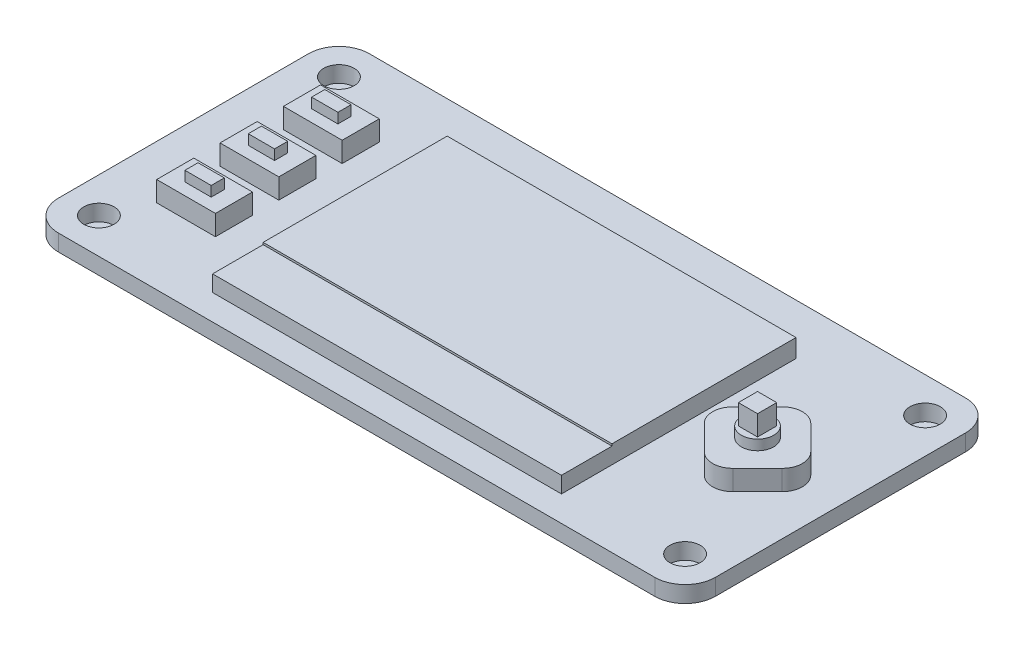
SolidWorks part; units mm, degrees
ref_plane "前视基准面" through (0, 0, 0) normal (0, 0, 1) x (1, 0, 0)
ref_plane "上视基准面" through (0, 0, 0) normal (0, 1, 0) x (1, 0, 0)
ref_plane "右视基准面" through (0, 0, 0) normal (1, 0, 0) x (0, 0, -1)
sketch "草图1" plane through (0, 0, 0) normal (0, 1, 0) x (1, 0, 0)
  line L1 (-29.5, 15.375) -> (29.5, 15.375)
  line L2 (-32.5, 12.375) -> (-32.5, -12.375)
  line L3 (-29.5, -15.375) -> (29.5, -15.375)
  line L4 (32.5, 12.375) -> (32.5, -12.375)
  line L5 (-32.5, 15.375) -> (32.5, -15.375) construction
  line L6 (-32.5, -15.375) -> (32.5, 15.375) construction
  arc A0 (-32.5, -12.375) -> (-29.5, -15.375) centre (-29.5, -12.375) ccw
  arc A1 (29.5, -15.375) -> (32.5, -12.375) centre (29.5, -12.375) ccw
  arc A2 (29.5, 15.375) -> (32.5, 12.375) centre (29.5, 12.375) cw
  arc A3 (-29.5, 15.375) -> (-32.5, 12.375) centre (-29.5, 12.375) ccw
  point P0 (0, 0)
  dimension "D3" = 3
  dimension "D1" = 30.75
  dimension "D2" = 65
extrude "凸台-拉伸1" add sketch "草图1" along normal blind 1.63
sketch "草图2" plane through (0, 1.63, 0) normal (0, 1, 0) x (1, 0, 0)
  line L0 (29.5, 15.375) -> (-29.5, 15.375) construction
  line L2 (-32.5, 12.375) -> (-32.5, -12.375) construction
  line L3 (-29.5, -15.375) -> (29.5, -15.375) construction
  line L4 (32.5, -12.375) -> (32.5, 12.375) construction
  circle A0 centre (-29, 11.875) radius 1.5
  circle A1 centre (-29, -11.875) radius 1.5
  circle A2 centre (29, -11.875) radius 1.5
  circle A3 centre (29, 11.875) radius 1.5
  dimension "D1" = 3
  dimension "D2" = 3.5
  dimension "D3" = 3.5
  dimension "D4" = 3.5
  dimension "D5" = 3.5
extrude "切除-拉伸1" cut sketch "草图2" against normal blind 1.6
sketch "草图3" plane through (0, 1.63, 0) normal (0, 1, 0) x (1, 0, 0)
  line L0 (-29.5, -15.375) -> (29.5, -15.375) construction
  line L1 (-16.78, 10.365) -> (17.74, 10.365)
  line L2 (-16.78, 10.365) -> (-16.78, -12.845)
  line L3 (-16.78, -12.845) -> (17.74, -12.845)
  line L4 (17.74, 10.365) -> (17.74, -12.845)
  line L7 (32.5, -12.375) -> (32.5, 12.375) construction
  dimension "D1" = 23.21
  dimension "D2" = 34.52
  dimension "D3" = 2.53
  dimension "D4" = 14.76
sketch "草图4" plane through (0, 1.63, 0) normal (0, 1, 0) x (1, 0, 0)
  line L0 (-29.5, -15.375) -> (29.5, -15.375) construction
  line L1 (-27.23, 8.285) -> (-21.42, 8.285)
  line L2 (-27.23, 8.285) -> (-27.23, 4.615)
  line L3 (-27.23, 4.615) -> (-21.42, 4.615)
  line L4 (-21.42, 8.285) -> (-21.42, 4.615)
  line L5 (-27.23, 2.015) -> (-21.42, 2.015)
  line L6 (-27.23, 2.015) -> (-27.23, -1.655)
  line L7 (-27.23, -1.655) -> (-21.42, -1.655)
  line L8 (-21.42, 2.015) -> (-21.42, -1.655)
  line L9 (-27.23, -4.255) -> (-21.42, -4.255)
  line L10 (-27.23, -4.255) -> (-27.23, -7.925)
  line L11 (-27.23, -7.925) -> (-21.42, -7.925)
  line L12 (-21.42, -4.255) -> (-21.42, -7.925)
  line L13 (-32.5, 12.375) -> (-32.5, -12.375) construction
  dimension "D1" = 5.81
  dimension "D2" = 3.67
  dimension "D3" = 2.6
  dimension "D4" = 2.6
  dimension "D5" = 7.45
  dimension "D6" = 5.27
sketch "草图5" plane through (0, 1.63, 0) normal (0, 1, 0) x (1, 0, 0)
  line L0 (26.0247, 3.5383) -> (28.4642, 1.0987)
  line L1 (23.1963, 3.5383) -> (20.7567, 1.0987)
  line L2 (28.4642, -1.7297) -> (26.0247, -4.1692)
  line L3 (20.7567, -1.7297) -> (23.1963, -4.1692)
  line L4 (32.5, -12.375) -> (32.5, 12.375) construction
  line L5 (-29.5, -15.375) -> (29.5, -15.375) construction
  arc A0 (26.0247, -4.1692) -> (23.1963, -4.1692) centre (24.6105, -2.755) cw
  arc A1 (20.7567, 1.0987) -> (20.7567, -1.7297) centre (22.171, -0.3155) ccw
  arc A2 (23.1963, 3.5383) -> (26.0247, 3.5383) centre (24.6105, 2.124) cw
  arc A3 (28.4642, 1.0987) -> (28.4642, -1.7297) centre (27.05, -0.3155) cw
  point P8 (19.3425, -0.3155)
  point P11 (24.6105, 4.9525)
  point P14 (29.8784, -0.3155)
  point P15 (29.05, -0.3155)
  point P18 (24.6105, -4.755)
  dimension "D3" = 2
  dimension "D1" = 7.45
  dimension "D2" = 7.45
  dimension "D4" = 3.45
  dimension "D5" = 10.62
extrude "凸台-拉伸2" add sketch "草图3" along normal blind 1.8
extrude "凸台-拉伸3" add sketch "草图5" along normal blind 2
extrude "凸台-拉伸4" add sketch "草图4" along normal blind 2
sketch "草图7" plane through (0, 3.63, 0) normal (0, 1, 0) x (1, 0, 0)
  line L0 (-21.42, 8.285) -> (-27.23, 8.285) construction
  line L1 (-25.625, 7.1) -> (-23.025, 7.1)
  line L2 (-25.625, 7.1) -> (-25.625, 5.8)
  line L3 (-25.625, 5.8) -> (-23.025, 5.8)
  line L4 (-23.025, 7.1) -> (-23.025, 5.8)
  line L5 (-25.625, 7.1) -> (-23.025, 5.8) construction
  line L6 (-25.625, 5.8) -> (-23.025, 7.1) construction
  line L7 (-25.625, 0.83) -> (-23.025, 0.83)
  line L8 (-25.625, 0.83) -> (-25.625, -0.47)
  line L9 (-25.625, -0.47) -> (-23.025, -0.47)
  line L10 (-23.025, 0.83) -> (-23.025, -0.47)
  line L11 (-25.625, 0.83) -> (-23.025, -0.47) construction
  line L12 (-25.625, -0.47) -> (-23.025, 0.83) construction
  line L13 (-25.625, -5.44) -> (-23.025, -5.44)
  line L14 (-25.625, -5.44) -> (-25.625, -6.74)
  line L15 (-25.625, -6.74) -> (-23.025, -6.74)
  line L16 (-23.025, -5.44) -> (-23.025, -6.74)
  line L17 (-25.625, -5.44) -> (-23.025, -6.74) construction
  line L18 (-25.625, -6.74) -> (-23.025, -5.44) construction
  line L19 (-27.23, -4.255) -> (-27.23, -7.925) construction
  line L20 (-27.23, 2.015) -> (-27.23, -1.655) construction
  line L21 (-27.23, 8.285) -> (-27.23, 4.615) construction
  point P0 (-24.325, 6.45)
  point P5 (-24.325, 0.18)
  point P10 (-24.325, -6.09)
  point P18 (-24.325, 8.285)
  point P22 (-27.23, -6.09)
  point P26 (-27.23, 0.18)
  point P30 (-27.23, 6.45)
  dimension "D1" = 2.6
  dimension "D2" = 1.3
extrude "凸台-拉伸5" add sketch "草图7" along normal blind 1
sketch "草图8" plane through (0, 0, 0) normal (0, -1, 0) x (1, 0, 0)
  line L0 (29.5, -15.375) -> (-29.5, -15.375) construction
  line L1 (-25.7, -8.735) -> (25.3, -8.735)
  line L2 (-25.7, -8.735) -> (-25.7, -13.735)
  line L3 (-25.7, -13.735) -> (25.3, -13.735)
  line L4 (25.3, -8.735) -> (25.3, -13.735)
  line L5 (32.5, 12.375) -> (32.5, -12.375) construction
  dimension "D1" = 5
  dimension "D2" = 51
  dimension "D3" = 1.64
  dimension "D4" = 7.2
extrude "凸台-拉伸6" add sketch "草图8" along normal blind 3.68
sketch "草图9" plane through (0, 3.63, 0) normal (0, 1, 0) x (1, 0, 0)
  line L1 (23.6605, 0.6345) -> (25.5605, 0.6345)
  line L2 (23.6605, 0.6345) -> (23.6605, -1.2655)
  line L3 (23.6605, -1.2655) -> (25.5605, -1.2655)
  line L4 (25.5605, 0.6345) -> (25.5605, -1.2655)
  line L5 (23.6605, 0.6345) -> (25.5605, -1.2655) construction
  line L6 (23.6605, -1.2655) -> (25.5605, 0.6345) construction
  arc A0 (28.4642, -1.7297) -> (28.4642, 1.0987) centre (27.05, -0.3155) ccw construction
  arc A1 (26.0247, 3.5383) -> (23.1963, 3.5383) centre (24.6105, 2.124) ccw construction
  point P0 (24.6105, -0.3155)
  point P11 (29.05, -0.3155)
  point P16 (24.6105, 4.124)
  dimension "D1" = 1.9
extrude "凸台-拉伸7" add sketch "草图9" along normal blind 3
sketch "草图10" plane through (0, 3.63, 0) normal (0, 1, 0) x (1, 0, 0)
  line L0 (25.5605, 0.6345) -> (23.6605, 0.6345) construction
  line L2 (25.5605, -1.2655) -> (25.5605, 0.6345) construction
  circle A0 centre (24.6105, -0.3155) radius 1.6
  point P5 (24.6105, 0.6345)
  point P11 (25.5605, -0.3155)
  dimension "D1" = 3.2
extrude "凸台-拉伸8" add sketch "草图10" along normal blind 1
sketch "草图11" plane through (0, 3.43, 0) normal (0, 1, 0) x (1, 0, 0)
  line L0 (17.74, -12.845) -> (17.74, 10.365) construction
  line L1 (-16.78, -12.845) -> (17.74, -12.845)
  line L2 (-16.78, -12.845) -> (-16.78, -7.845)
  line L3 (-16.78, -7.845) -> (17.74, -7.845)
  line L4 (17.74, -12.845) -> (17.74, -7.845)
  dimension "D1" = 5
extrude "切除-拉伸2" cut sketch "草图11" against normal blind 0.2
